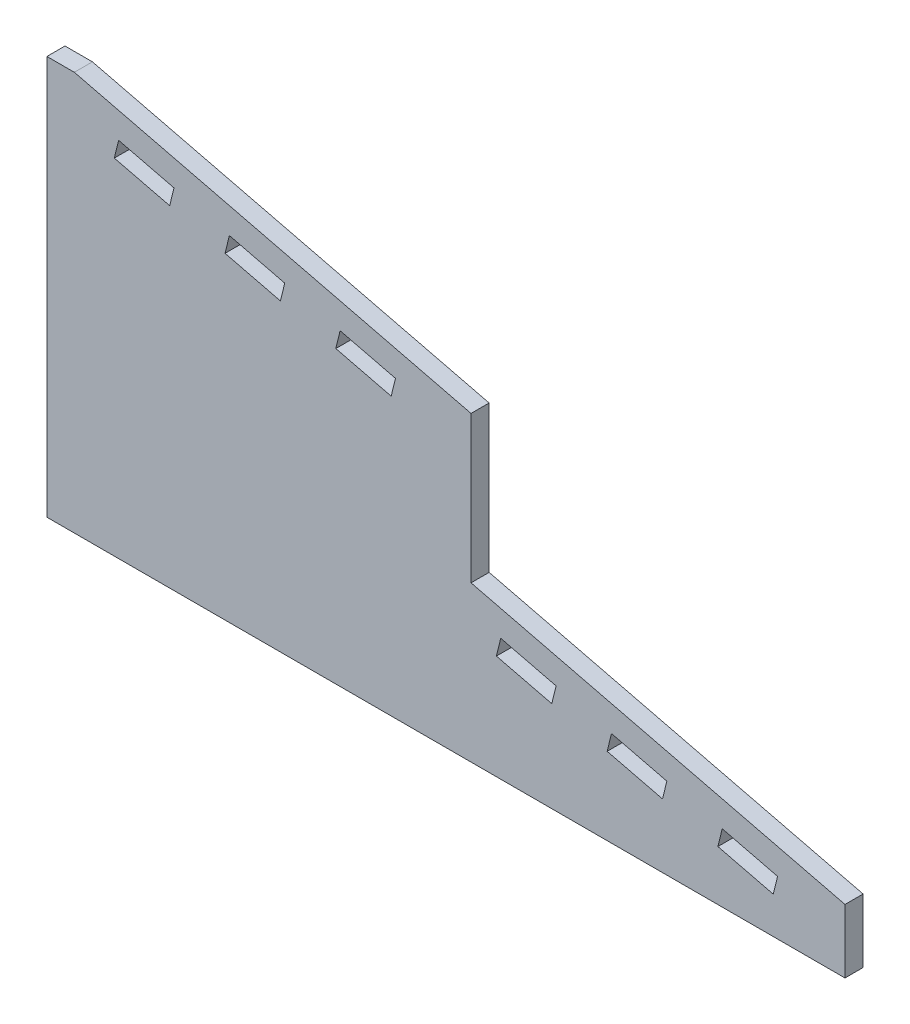
SolidWorks part; units mm, degrees
ref_plane "Front Plane" through (0, 0, 0) normal (0, 0, 1) x (1, 0, 0)
ref_plane "Top Plane" through (0, 0, 0) normal (0, 1, 0) x (1, 0, 0)
ref_plane "Right Plane" through (0, 0, 0) normal (1, 0, 0) x (0, 0, -1)
sketch "Sketch1" plane through (0, 0, 0) normal (0, 0, 1) x (1, 0, 0)
  line L1 (0, 0) -> (140, 0)
  line L2 (0, 0) -> (0, 70)
  line L3 (0, 70) -> (140, 70)
  line L4 (140, 0) -> (140, 70)
  dimension "D1" = 70
  dimension "D2" = 140
extrude "Boss-Extrude1" add sketch "Sketch1" along normal blind 3.175
sketch "Sketch3" plane through (0, 0, 3.175) normal (0, 0, 1) x (1, 0, 0)
  line L0 (0, 65) -> (72.9714, 47.1417) construction
  line L1 (0, 70) -> (0, 0) construction
  line L2 (72.9714, 47.1417) -> (67.0286, 22.8583) construction
  line L3 (67.0286, 22.8583) -> (140, 5) construction
  line L4 (140, 0) -> (140, 70) construction
  line L5 (140, 70) -> (0, 70) construction
  line L6 (0, 35) -> (140, 35) construction
  point P4 (70, 35)
  dimension "D1" = 5
  dimension "D2" = 5
  dimension "D3" = 25
sketch "Sketch4" plane through (0, 0, 3.175) normal (0, 0, 1) x (1, 0, 0)
  line L0 (12.5797, 63.5557) -> (11.825, 60.4717)
  line L1 (11.825, 60.4717) -> (21.5383, 58.0946)
  line L2 (21.5383, 58.0946) -> (22.2931, 61.1786)
  line L3 (22.2931, 61.1786) -> (12.5797, 63.5557)
  line L4 (0, 65) -> (72.9714, 47.1417) construction
  line L5 (41.7198, 56.4243) -> (32.0064, 58.8014)
  line L6 (32.0064, 58.8014) -> (31.2517, 55.7174)
  line L7 (31.2517, 55.7174) -> (40.965, 53.3403)
  line L8 (40.965, 53.3403) -> (41.7198, 56.4243)
  line L9 (61.1465, 51.67) -> (51.4331, 54.0471)
  line L10 (51.4331, 54.0471) -> (50.6784, 50.9631)
  line L11 (50.6784, 50.9631) -> (60.3917, 48.586)
  line L12 (60.3917, 48.586) -> (61.1465, 51.67)
  line L13 (36.8631, 57.6128) -> (36.1083, 54.5288) construction
  line L14 (0, 0) -> (140, 70) construction
  line L15 (67.0286, 22.8583) -> (140, 5) construction
  line L16 (67.0286, 22.8583) -> (140, 5) construction
  line L18 (118.4617, 11.9054) -> (128.175, 9.5283)
  line L30 (128.175, 9.5283) -> (127.4203, 6.4443)
  line L31 (127.4203, 6.4443) -> (117.7069, 8.8214)
  line L32 (117.7069, 8.8214) -> (118.4617, 11.9054)
  line L33 (98.2802, 13.5757) -> (99.035, 16.6597)
  line L34 (99.035, 16.6597) -> (108.7483, 14.2826)
  line L35 (108.7483, 14.2826) -> (107.9936, 11.1986)
  line L36 (107.9936, 11.1986) -> (98.2802, 13.5757)
  line L37 (78.8535, 18.33) -> (79.6083, 21.414)
  line L38 (79.6083, 21.414) -> (89.3216, 19.0369)
  line L39 (89.3216, 19.0369) -> (88.5669, 15.9529)
  line L40 (88.5669, 15.9529) -> (78.8535, 18.33)
  line L41 (103.8917, 15.4712) -> (103.1369, 12.3872) construction
  point P6 (12.2023, 62.0137)
  point P17 (36.4857, 56.0708)
  point P18 (36.4857, 56.0708)
  point P27 (118.0843, 10.3634)
  point P29 (79.2309, 19.872)
  point P40 (103.5143, 13.9292)
  point P42 (103.5143, 13.9292)
  point P43 (112.5224, 10.0903)
  point P44 (103.5143, 13.9292)
  dimension "D2" = 3.175
  dimension "D3" = 10
  dimension "D4" = 10
  dimension "D5" = 3.175
  dimension "D6" = 10
  dimension "D7" = 3
  dimension "D8" = 10
  dimension "D1" = 3
extrude "Cut-Extrude1" cut sketch "Sketch4" against normal through all
sketch "Sketch5" plane through (0, 0, 3.175) normal (0, 0, 1) x (1, 0, 0)
  line L5 (1.4263, 70.828) -> (74.3977, 52.9697)
  line L6 (4.8096, 70) -> (74.3977, 52.9697)
  line L7 (74.3977, 52.9697) -> (74.3977, 27.2319)
  line L8 (68.4549, 28.6863) -> (141.4263, 10.828)
  line L9 (74.3977, 27.2319) -> (140, 11.1771)
  line L14 (0, 70) -> (0, 0)
  line L15 (0, 0) -> (140, 0)
  line L16 (140, 0) -> (140, 70)
  line L17 (140, 70) -> (0, 70)
  line L20 (140, 11.1771) -> (140, 70)
  line L21 (140, 70) -> (4.8096, 70)
  dimension "D1" = 6
  dimension "D2" = 6
  dimension "D3" = 0
extrude "Cut-Extrude2" cut sketch "Sketch5" against normal through all
